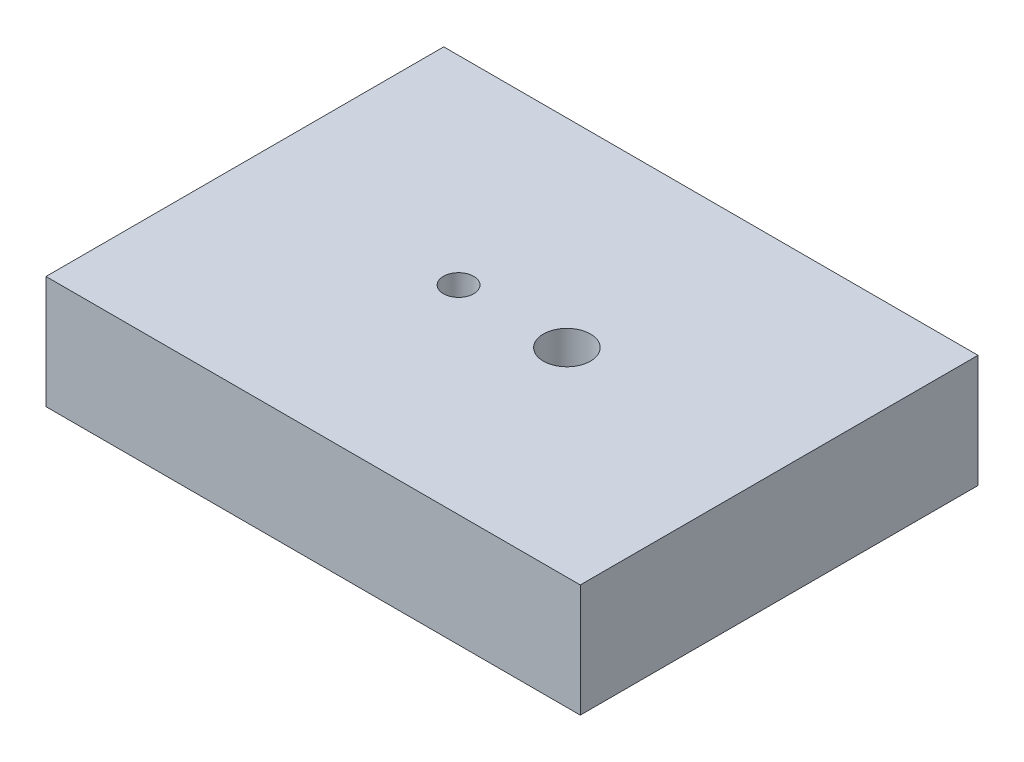
SolidWorks part; units mm, degrees
ref_plane "Спереди" through (0, 0, 0) normal (0, 0, 1) x (1, 0, 0)
ref_plane "Сверху" through (0, 0, 0) normal (0, 1, 0) x (1, 0, 0)
ref_plane "Справа" through (0, 0, 0) normal (1, 0, 0) x (0, 0, -1)
sketch "Эскиз1" plane through (0, 0, 0) normal (0, 1, 0) x (1, 0, 0)
  line L0 (0, -33.5) -> (90, -33.5) construction
  line L1 (0, 0) -> (90, 0)
  line L2 (0, 0) -> (0, -67)
  line L3 (0, -67) -> (90, -67)
  line L4 (90, 0) -> (90, -67)
  line L5 (45, 0) -> (45, -67) construction
  line L6 (36, 0) -> (36, -67) construction
  line L7 (54.25, 0) -> (54.25, -67) construction
  dimension "D1" = 90
  dimension "D2" = 67
  dimension "D3" = 36
  dimension "D4" = 54.25
extrude "Бобышка-Вытянуть1" add sketch "Эскиз1" along normal blind 19
sketch "Эскиз2" plane through (0, 0, 0) normal (0, -1, 0) x (1, 0, 0)
  line L0 (36, 0) -> (36, 67) construction
  line L1 (54.25, 0) -> (54.25, 67) construction
  line L2 (0, 33.5) -> (90, 33.5) construction
  circle A0 centre (36, 33.5) radius 2.5
  circle A1 centre (54.25, 33.5) radius 3.75
  dimension "D1" = 5
  dimension "D2" = 7.5
hole_wizard "Отверстие обработанное метчиком 1/4-201" positions "Трехмерный эскиз1" profile "Эскиз3" tap size "1/4-20" standard "Ansi Inch" end condition through all
sketch3d "Трехмерный эскиз1"
  point P0 (36, 0, 33.5)
sketch "Эскиз3" plane through (36, 0, 33.5) normal (1, 0, 0) x (0, 0, -1)
  line L0 (0, 0) -> (0, 19)
  line L1 (0, 19) -> (2.5527, 19)
  line L2 (2.5527, 19) -> (2.5527, 0)
  line L5 (2.5527, 0) -> (0, 0)
  line L11 (0, -6.35) -> (0, 107.95) construction
  dimension "Диаметр резьбы" = 5.1054
  dimension "Глубина проходного сверла" = 19
hole_wizard "Отверстие обработанное метчиком 3/8-161" positions "Трехмерный эскиз2" profile "Эскиз4" tap size "3/8-16" standard "Ansi Inch" end condition through all
sketch3d "Трехмерный эскиз2"
  point P0 (54.25, 0, 33.5)
sketch "Эскиз4" plane through (54.25, 0, 33.5) normal (1, 0, 0) x (0, 0, -1)
  line L0 (0, 0) -> (0, 19)
  line L1 (0, 19) -> (3.9687, 19)
  line L2 (3.9687, 19) -> (3.9687, 0)
  line L5 (3.9687, 0) -> (0, 0)
  line L11 (0, -6.35) -> (0, 107.95) construction
  dimension "Диаметр резьбы" = 7.9375
  dimension "Глубина проходного сверла" = 19
